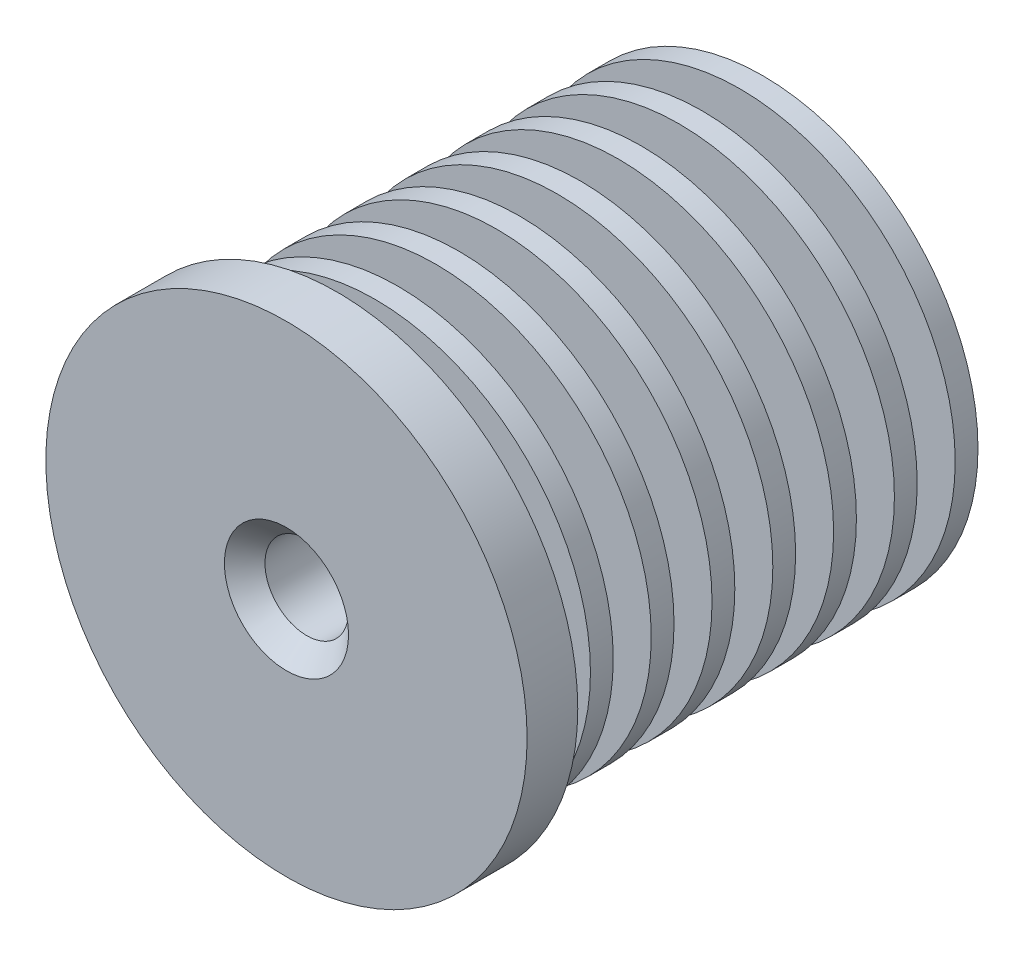
SolidWorks part; units mm, degrees
material "1060 Alloy"
ref_plane "Front Plane" through (0, 0, 0) normal (0, 0, 1) x (1, 0, 0)
ref_plane "Top Plane" through (0, 0, 0) normal (0, 1, 0) x (1, 0, 0)
ref_plane "Right Plane" through (0, 0, 0) normal (1, 0, 0) x (0, 0, -1)
sketch "Sketch2" plane through (0, 0, 0) normal (0, 1, 0) x (1, 0, 0)
  line L0 (0, 0) -> (0, 11.6) construction
  line L1 (1.65, 18.8) -> (1.65, 0)
  line L4 (9.5, 2) -> (6, 2)
  line L5 (6, 2) -> (6, 3.5)
  line L6 (6, 3.5) -> (8.5, 3.5)
  line L7 (8.5, 3.5) -> (8.5, 4.4)
  line L8 (8.5, 4.4) -> (3.5, 4.4)
  line L9 (3.5, 4.4) -> (3.5, 5.9)
  line L10 (3.5, 5.9) -> (8.5, 5.9)
  line L11 (8.5, 5.9) -> (8.5, 6.8)
  line L12 (8.5, 6.8) -> (3.5, 6.8)
  line L13 (3.5, 6.8) -> (3.5, 8.3)
  line L14 (3.5, 8.3) -> (8.5, 8.3)
  line L15 (8.5, 8.3) -> (8.5, 9.2)
  line L16 (8.5, 9.2) -> (3.5, 9.2)
  line L17 (3.5, 9.2) -> (3.5, 10.7)
  line L18 (3.5, 10.7) -> (8.5, 10.7)
  line L19 (8.5, 10.7) -> (8.5, 11.6)
  line L20 (8.5, 11.6) -> (3.5, 11.6)
  line L21 (1.65, 0) -> (9.5, 0)
  line L22 (9.5, 0) -> (9.5, 2)
  line L23 (3.5, 11.6) -> (3.5, 13.1)
  line L24 (3.5, 13.1) -> (8.5, 13.1)
  line L25 (8.5, 13.1) -> (8.5, 14)
  line L26 (8.5, 14) -> (3.5, 14)
  line L27 (3.5, 14) -> (3.5, 15.5)
  line L28 (3.5, 15.5) -> (8.5, 15.5)
  line L29 (8.5, 15.5) -> (8.5, 16.4)
  line L30 (8.5, 16.4) -> (3.5, 16.4)
  line L31 (3.5, 16.4) -> (3.5, 17.9)
  line L32 (3.5, 17.9) -> (8.5, 17.9)
  line L33 (8.5, 17.9) -> (8.5, 18.8)
  line L34 (8.5, 18.8) -> (1.65, 18.8)
  dimension "D1" = 17
  dimension "D2" = 0.9
  dimension "D3" = 0.9
  dimension "D4" = 3.3
  dimension "D5" = 7
  dimension "D6" = 12
  dimension "D7" = 19
  dimension "D8" = 1.5
  dimension "D9" = 2
revolve "Revolve1" add sketch "Sketch2" angle 360 about L0
cosmetic thread "Cosmetic Thread1" parameters "D2"=4
chamfer "Chamfer1" distance 0.8 angle 45 1 edges at (1.65, 0, 0)
